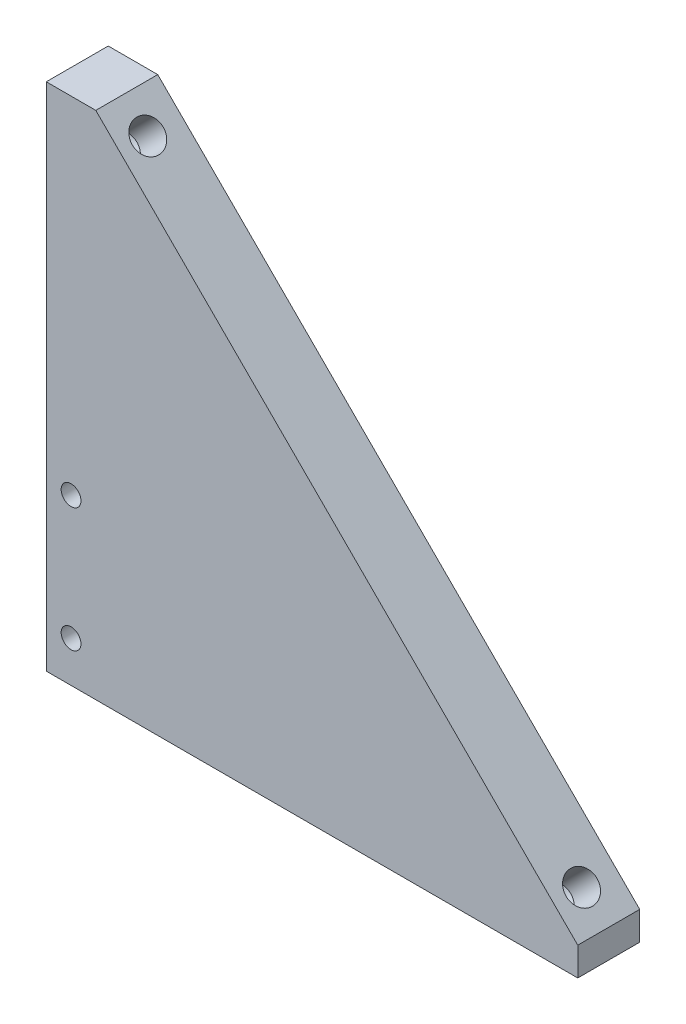
SolidWorks part; units mm, degrees
material "A286 Iron Base Superalloy"
ref_plane "Front Plane" through (0, 0, 0) normal (0, 0, 1) x (1, 0, 0)
ref_plane "Top Plane" through (0, 0, 0) normal (0, 1, 0) x (1, 0, 0)
ref_plane "Right Plane" through (0, 0, 0) normal (1, 0, 0) x (0, 0, -1)
sketch "Sketch2" plane through (0, 0, 0) normal (0, 0, 1) x (1, 0, 0)
  line L0 (-19.4454, 19.4454) -> (26.5165, -26.5165)
  line L1 (-19.4454, -26.5165) -> (26.5165, -26.5165)
  line L2 (-19.4454, -26.5165) -> (-19.4454, 19.4454)
  line L6 (-19.4454, 19.4454) -> (26.5165, -26.5165) construction
  point P0 (0, 0)
  dimension "D1" = 65
  dimension "D2" = 45
  dimension "D3" = 45.9619
  dimension "D4" = 45.9619
extrude "Boss-Extrude1" add sketch "Sketch2" along normal blind 5
sketch "Sketch3" plane through (0, 0, 0) normal (0.7071, 0.7071, 0) x (0, 0, -1)
  line L3 (0, -37.5) -> (0, 27.5) construction
  line L4 (-5, 27.5) -> (0, 27.5) construction
  line L6 (-5, -37.5) -> (0, -37.5) construction
  circle A0 centre (-2.75, -29.75) radius 1.5
  circle A1 centre (-2.75, 19.75) radius 1.5
  dimension "D3" = 3
  dimension "D4" = 3
  dimension "D1" = 2.75
  dimension "D2" = 7.75
  dimension "D5" = 7.75
  dimension "D6" = 2.75
hole_wizard "M3x0.5 Tapped Hole1" positions "Sketch5" profile "Sketch4" tap size "M3x0.5" standard "ANSI Metric"
sketch "Sketch5" plane through (0, 0, 0) normal (0.7071, 0.7071, 0) x (0, 0, -1)
  point P0 (-2.75, 19.75)
  point P3 (-2.75, -29.75)
sketch "Sketch4" plane through (-13.9654, 13.9654, 2.75) normal (0, 0, 1) x (-0.7071, 0.7071, 0)
  line L0 (0, 0) -> (0, 3.7511)
  line L1 (0, 3.7511) -> (1.25, 3)
  line L2 (1.25, 3) -> (1.25, 0)
  line L5 (1.25, 0) -> (0, 0)
  line L10 (0, 3.7511) -> (-1.25, 3) construction
  line L11 (0, -6.35) -> (0, 107.95) construction
  dimension "Tap Drill Dia." = 2.5
  dimension "Tap Drill Depth" = 3
  dimension "Drill Angle" = 118
cosmetic thread "Hole Thread1" parameters "D1"=3, "D2"=3
cosmetic thread "Hole Thread2" parameters "D1"=3, "D2"=3
sketch "Sketch6" plane through (0, 0, 5) normal (0, 0, 1) x (1, 0, 0)
  line L0 (-19.4454, 19.4454) -> (-15.9099, 15.9099)
  line L1 (26.5165, -26.5165) -> (-19.4454, 19.4454) construction
  line L2 (-15.9099, 15.9099) -> (-14.4957, 17.3241)
  line L3 (-14.4957, 17.3241) -> (-18.0312, 20.8597)
  line L4 (-18.0312, 20.8597) -> (-19.4454, 19.4454)
  line L5 (26.5165, -26.5165) -> (22.981, -22.981)
  line L6 (22.981, -22.981) -> (24.3952, -21.5668)
  line L7 (24.3952, -21.5668) -> (27.9307, -25.1023)
  line L8 (27.9307, -25.1023) -> (26.5165, -26.5165)
  dimension "D1" = 2
  dimension "D2" = 5
  dimension "D3" = 2
  dimension "D4" = 5
extrude "Boss-Extrude2" add sketch "Sketch6" against normal through all
sketch "Sketch7" plane through (0, 0, 5) normal (0, 0, 1) x (1, 0, 0)
  line L0 (-18.0312, 20.8597) -> (-14.4957, 17.3241)
  line L1 (-14.4957, 17.3241) -> (-19.4454, 12.3744)
  line L2 (-19.4454, 19.4454) -> (-19.4454, -26.5165) construction
  line L3 (-19.4454, 12.3744) -> (-19.4454, 19.4454)
  line L4 (-19.4454, 19.4454) -> (-18.0312, 20.8597)
  line L5 (24.3952, -21.5668) -> (19.4454, -26.5165)
  line L6 (-19.4454, -26.5165) -> (26.5165, -26.5165) construction
  line L7 (19.4454, -26.5165) -> (26.5165, -26.5165)
  line L8 (26.5165, -26.5165) -> (27.9307, -25.1023)
  line L9 (27.9307, -25.1023) -> (24.3952, -21.5668)
extrude "Cut-Extrude1" cut sketch "Sketch7" against normal through all
sketch "Sketch11" plane through (0, 0, 0) normal (0, 0, -1) x (-1, 0, 0)
  line L0 (-19.4454, -26.5165) -> (-22.981, -26.5165)
  line L1 (-22.981, -26.5165) -> (-22.981, -22.981)
  line L2 (-22.981, -22.981) -> (-19.4454, -26.5165)
  line L3 (19.4454, 12.3744) -> (19.4454, 15.9099)
  line L4 (19.4454, 15.9099) -> (15.9099, 15.9099)
  line L5 (15.9099, 15.9099) -> (19.4454, 12.3744)
extrude "Boss-Extrude3" add sketch "Sketch11" against normal through all
sketch "Sketch12" plane through (0, 0, 5) normal (0, 0, 1) x (1, 0, 0)
  line L1 (-19.4454, -26.5165) -> (22.981, -26.5165)
  line L2 (-19.4454, -26.5165) -> (-19.4454, -26.9765)
  line L3 (-19.4454, -26.9765) -> (22.981, -26.9765)
  line L4 (22.981, -26.5165) -> (22.981, -26.9765)
  dimension "D1" = 0.46
extrude "Boss-Extrude4" add sketch "Sketch12" against normal through all
sketch "Sketch13" plane through (0, 0, 5) normal (0, 0, 1) x (1, 0, 0)
  line L1 (-19.4454, 15.9099) -> (-19.9054, 15.9099)
  line L2 (-19.4454, 15.9099) -> (-19.4454, -26.9765)
  line L3 (-19.4454, -26.9765) -> (-19.9054, -26.9765)
  line L4 (-19.9054, 15.9099) -> (-19.9054, -26.9765)
  dimension "D1" = 0.46
extrude "Boss-Extrude5" add sketch "Sketch13" against normal through all
sketch "Sketch14" plane through (0, 0, 0) normal (0, 0, -1) x (-1, 0, 0)
  line L1 (19.9054, 15.9099) -> (19.9054, -26.9765) construction
  line L2 (19.9054, -26.9765) -> (-22.981, -26.9765) construction
  circle A0 centre (17.9054, -11.9765) radius 1.5
  circle A1 centre (17.9054, -21.9765) radius 1.5
  dimension "D1" = 3
  dimension "D2" = 3
  dimension "D3" = 5
  dimension "D4" = 10
  dimension "D5" = 2
  dimension "D6" = 2
hole_wizard "M2x0.4 Tapped Hole1" positions "Sketch18" profile "Sketch17" tap size "M2x0.4" standard "ANSI Metric" end condition through all
sketch "Sketch18" plane through (0, 0, 0) normal (0, 0, -1) x (-1, 0, 0)
  point P0 (17.9054, -11.9765)
  point P3 (17.9054, -21.9765)
sketch "Sketch17" plane through (-17.9054, -11.9765, 0) normal (1, 0, 0) x (0, 1, 0)
  line L0 (0, 0) -> (0, 5)
  line L1 (0, 5) -> (0.8, 5)
  line L2 (0.8, 5) -> (0.8, 0)
  line L5 (0.8, 0) -> (0, 0)
  line L11 (0, -6.35) -> (0, 107.95) construction
  dimension "Thru Tap Drill Dia." = 1.6
  dimension "Thru Tap Drill Depth" = 5
cosmetic thread "Hole Thread3" parameters "D2"=2
cosmetic thread "Hole Thread4" parameters "D2"=2
sketch "Sketch19" plane through (0, 0, 0) normal (0, 0, -1) x (-1, 0, 0)
  line L0 (-22.981, -22.981) -> (-22.981, -26.9765) construction
  line L1 (19.9054, -26.9765) -> (-22.981, -26.9765) construction
  circle A0 centre (-9.531, -24.9765) radius 1.5
  circle A1 centre (10.469, -24.9765) radius 1.5
  dimension "D1" = 3
  dimension "D2" = 3
  dimension "D3" = 13.45
  dimension "D4" = 20
  dimension "D5" = 2
  dimension "D6" = 2
sketch "Sketch20" plane through (0, 0, 5) normal (0, 0, 1) x (1, 0, 0)
  line L0 (-19.9054, 15.9099) -> (-19.9054, -26.9765) construction
  line L1 (22.981, -26.9765) -> (-19.9054, -26.9765)
  line L2 (22.981, -26.9765) -> (22.981, -25.2765)
  line L3 (22.981, -25.2765) -> (-19.9054, -25.2765)
  line L4 (-19.9054, -26.9765) -> (-19.9054, -25.2765)
  dimension "D1" = 1.7
extrude "Cut-Extrude2" cut sketch "Sketch20" against normal through all
sketch "Sketch21" plane through (0, -25.2765, 0) normal (0, -1, 0) x (1, 0, 0)
  line L0 (-19.9054, 0) -> (-19.9054, 5) construction
  circle A0 centre (-7.9054, 2.5) radius 1.5
  circle A1 centre (7.0946, 2.5) radius 1.5
  dimension "D1" = 3
  dimension "D2" = 3
  dimension "D3" = 15
  dimension "D4" = 12
hole_wizard "M3x0.5 Tapped Hole3" positions "Sketch23" profile "Sketch22" tap size "M3x0.5" standard "ANSI Metric"
sketch "Sketch23" plane through (0, -25.2765, 0) normal (0, -1, 0) x (-1, 0, 0)
  point P0 (7.9054, -2.5)
  point P3 (-7.0946, -2.5)
sketch "Sketch22" plane through (-7.9054, -25.2765, 2.5) normal (1, 0, 0) x (0, 0, -1)
  line L0 (0, 0) -> (0, 6.7511)
  line L1 (0, 6.7511) -> (1.25, 6)
  line L2 (1.25, 6) -> (1.25, 0)
  line L5 (1.25, 0) -> (0, 0)
  line L10 (0, 6.7511) -> (-1.25, 6) construction
  line L11 (0, -6.35) -> (0, 107.95) construction
  dimension "Tap Drill Dia." = 2.5
  dimension "Tap Drill Depth" = 6
  dimension "Drill Angle" = 118
cosmetic thread "Hole Thread5" parameters "D1"=6, "D2"=3
cosmetic thread "Hole Thread6" parameters "D1"=6, "D2"=3
